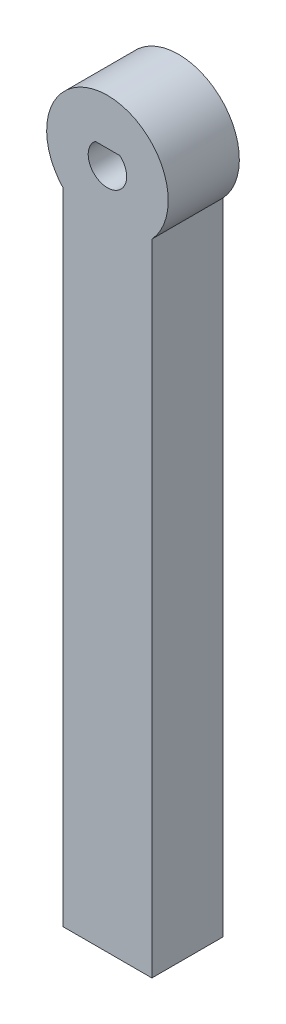
SolidWorks part; units mm, degrees
ref_plane "Front Plane" through (0, 0, 0) normal (0, 0, 1) x (1, 0, 0)
ref_plane "Top Plane" through (0, 0, 0) normal (0, 1, 0) x (1, 0, 0)
ref_plane "Right Plane" through (0, 0, 0) normal (1, 0, 0) x (0, 0, -1)
sketch "Sketch1" plane through (0, 0, 0) normal (0, 0, 1) x (1, 0, 0)
  line L0 (-20.4138, -49.5138) -> (-20.4138, 65.4862) construction
  line L1 (-27.9138, 58.4862) -> (-12.9138, 58.4862)
  line L2 (-27.9138, 58.4862) -> (-27.9138, -49.5138)
  line L3 (-27.9138, -49.5138) -> (-12.9138, -49.5138)
  line L4 (-12.9138, 58.4862) -> (-12.9138, -49.5138)
  circle A0 centre (-20.4138, 65.4862) radius 10.2591
  dimension "D1" = 108
  dimension "D2" = 15
  dimension "D3" = 115
  dimension "D4" = 7.5
extrude "Boss-Extrude1" add sketch "Sketch1" along normal blind 12
sketch "Sketch2" plane through (0, 0, 12) normal (0, 0, 1) x (1, 0, 0)
  circle A0 centre (-20.4138, 65.4862) radius 3.25
extrude "Cut-Extrude1" cut sketch "Sketch2" against normal blind 9
sketch "Sketch3" plane through (0, 0, 12) normal (0, 0, 1) x (1, 0, 0)
  line L0 (-22.4905, 67.9862) -> (-18.3372, 67.9862)
  circle A0 centre (-20.4138, 65.4862) radius 3.25 construction
  arc A1 (-22.4905, 67.9862) -> (-18.3372, 67.9862) centre (-20.4138, 65.4862) cw
  point P4 (-20.4138, 65.4862)
  dimension "D1" = 2.5
extrude "Boss-Extrude2" add sketch "Sketch3" against normal blind 9
